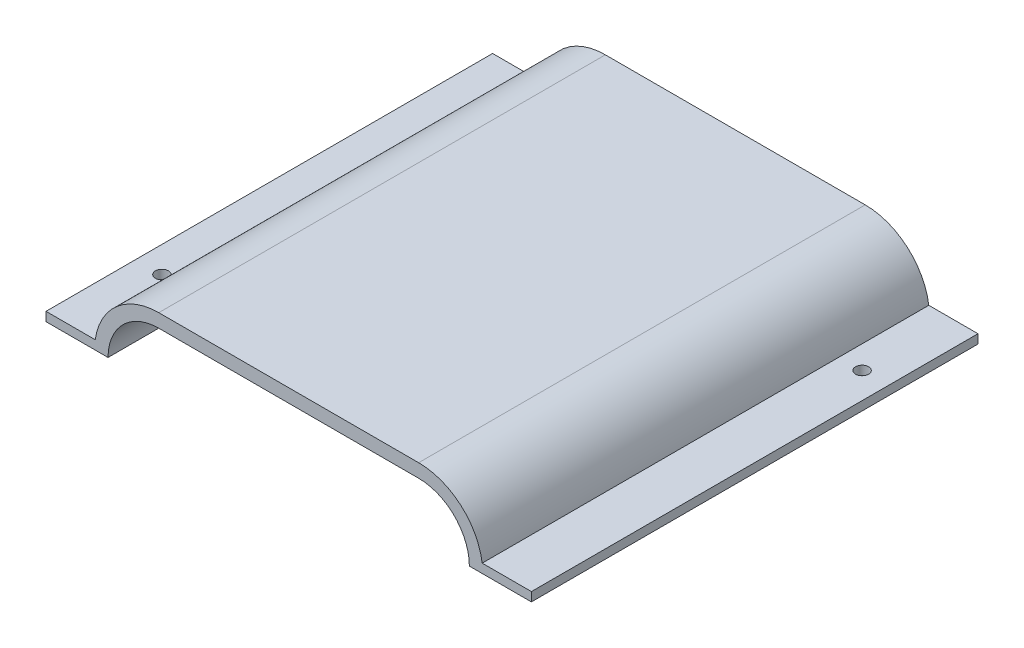
SolidWorks part; units mm, degrees
ref_plane "Front Plane" through (0, 0, 0) normal (0, 0, 1) x (1, 0, 0)
ref_plane "Top Plane" through (0, 0, 0) normal (0, 1, 0) x (1, 0, 0)
ref_plane "Right Plane" through (0, 0, 0) normal (1, 0, 0) x (0, 0, -1)
sketch "Sketch1" plane through (0, 0, 0) normal (0, 0, 1) x (1, 0, 0)
  line L0 (-28.95, 19.05) -> (28.95, 19.05) construction
  line L1 (-28.95, 30.1) -> (28.95, 30.1)
  line L2 (-28.95, 8) -> (28.95, 8)
  line L4 (0, 19.05) -> (0, 0) construction
  line L5 (-28.95, 30.35) -> (28.95, 30.35)
  line L6 (-28.95, 7.75) -> (28.95, 7.75)
  line L7 (-28.95, 33.35) -> (28.95, 33.35)
  line L8 (-28.95, 4.75) -> (28.95, 4.75)
  line L9 (-38.0268, 8) -> (38.0268, 8)
  line L10 (-43.25, 19.05) -> (43.25, 19.05)
  line L11 (-28.95, 4.75) -> (-50.25, 4.75)
  line L12 (-50.25, 4.75) -> (-50.25, 19.05)
  line L13 (-50.25, 19.05) -> (-43.25, 19.05)
  line L14 (50.25, 19.05) -> (43.25, 19.05)
  line L15 (28.95, 4.75) -> (50.25, 4.75)
  line L16 (50.25, 4.75) -> (50.25, 19.05)
  line L18 (-50.25, 19.05) -> (-54.0716, 19.05)
  line L19 (-54.0716, 19.05) -> (-54.0716, 21.05)
  line L20 (-54.0716, 21.05) -> (-40.0716, 21.05)
  line L21 (54.0716, 21.05) -> (40.0716, 21.05)
  line L22 (54.0716, 19.05) -> (54.0716, 21.05)
  line L23 (50.25, 19.05) -> (54.0716, 19.05)
  arc A0 (-28.95, 30.1) -> (-28.95, 8) centre (-28.95, 19.05) ccw
  arc A1 (28.95, 8) -> (28.95, 30.1) centre (28.95, 19.05) ccw
  arc A2 (28.95, 7.75) -> (28.95, 30.35) centre (28.95, 19.05) ccw
  arc A3 (-28.95, 30.35) -> (-28.95, 7.75) centre (-28.95, 19.05) ccw
  arc A4 (28.95, 4.75) -> (28.95, 33.35) centre (28.95, 19.05) ccw
  arc A5 (-28.95, 33.35) -> (-28.95, 4.75) centre (-28.95, 19.05) ccw
  point P2 (0, 19.05)
  point P29 (0, 19.05)
  dimension "D2" = 80
  dimension "D5" = 10
  dimension "D1" = 22.1
  dimension "D6" = 14
  dimension "D7" = 2
  dimension "D8" = 19.05
  dimension "D3" = 0.25
  dimension "D4" = 3
extrude "Boss-Extrude1" add sketch "Sketch1" along normal blind 99.5 contours L7 A5 L20 A3 L5 A2 L21 A4 | L20 A5 L10 A3 | A5 L20 L19 L18 L13 | L10 A4 L21 A2 | A4 L14 L23 L22 L21
sketch "Sketch3" plane through (0, 19.05, 0) normal (0, -1, 0) x (1, 0, 0)
  line L2 (-54.0716, 99.5) -> (-40.25, 99.5) construction
  line L3 (40.25, 0) -> (54.0716, 0) construction
  line L5 (-40.25, 99.5) -> (-40.25, 0) construction
  line L6 (40.25, 99.5) -> (40.25, 0) construction
  circle A0 centre (-48.25, 79.5) radius 1.45
  circle A1 centre (48.25, 20) radius 1.45
  point P8 (-47.1608, 99.5)
  dimension "D1" = 8
  dimension "D2" = 2.9
  dimension "D3" = 20
  dimension "D4" = 20
  dimension "D5" = 8
extrude "Cut-Extrude1" cut sketch "Sketch3" against normal up to surface (2 mm away) up to face at (-48.5905, 21.05, 49.75)
